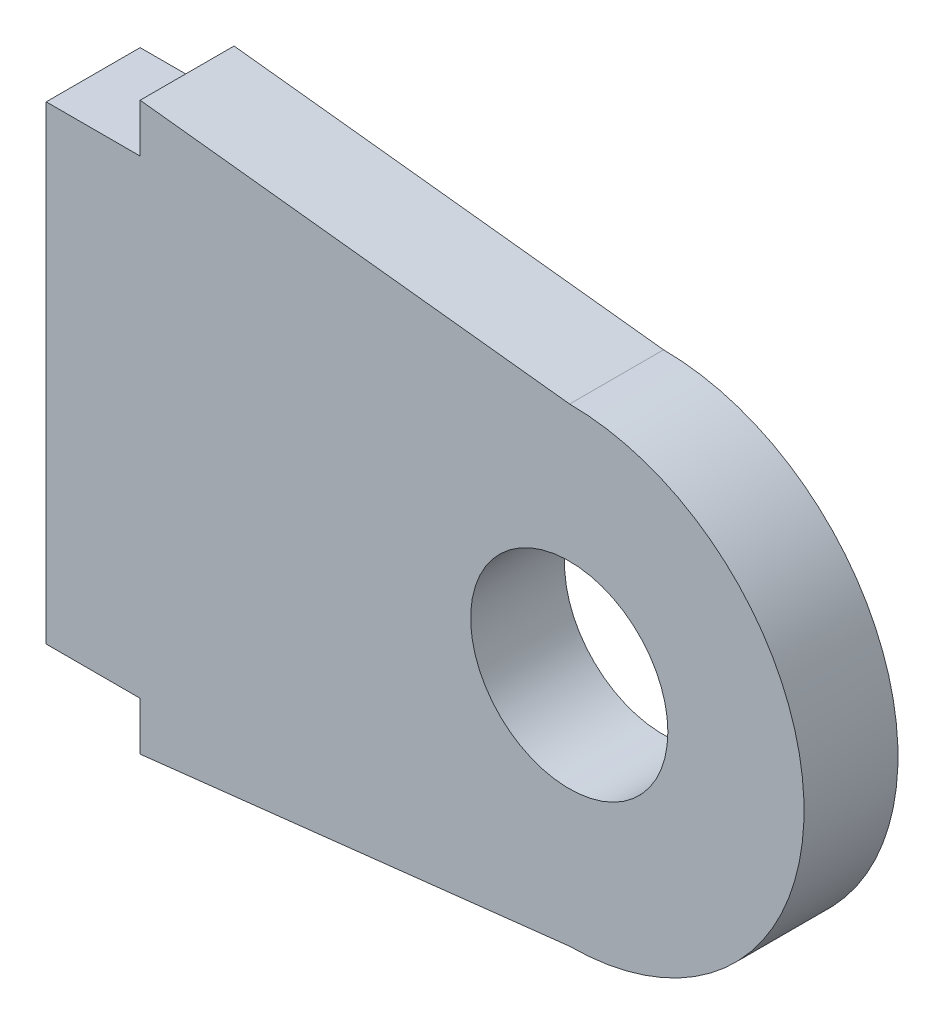
SolidWorks part; units mm, degrees
ref_plane "Alzado" through (0, 0, 0) normal (0, 0, 1) x (1, 0, 0)
ref_plane "Planta" through (0, 0, 0) normal (0, 1, 0) x (1, 0, 0)
ref_plane "Vista lateral" through (0, 0, 0) normal (1, 0, 0) x (0, 0, -1)
sketch "Croquis1" plane through (0, 0, 0) normal (0, 0, 1) x (1, 0, 0)
  line L0 (-2, 14.3781) -> (-2, -5.6219)
  line L1 (-2, -5.6219) -> (2, -5.6219)
  line L3 (2, 14.3781) -> (-2, 14.3781)
  line L4 (2, 14.3781) -> (2, 16.4374)
  line L5 (2, 16.4374) -> (20.2923, 14.3781)
  line L8 (2, -7.6812) -> (20.2923, -5.6219)
  line L9 (2, 16.4374) -> (2, 14.3781)
  line L10 (2, -7.6812) -> (2, -5.6219)
  arc A0 (20.26, -5.6219) -> (20.2923, 14.3781) centre (20.2761, 4.3781) ccw
  circle A2 centre (20.2761, 4.3781) radius 4.2
extrude "Saliente-Extruir1" add sketch "Croquis1" along normal blind 4
